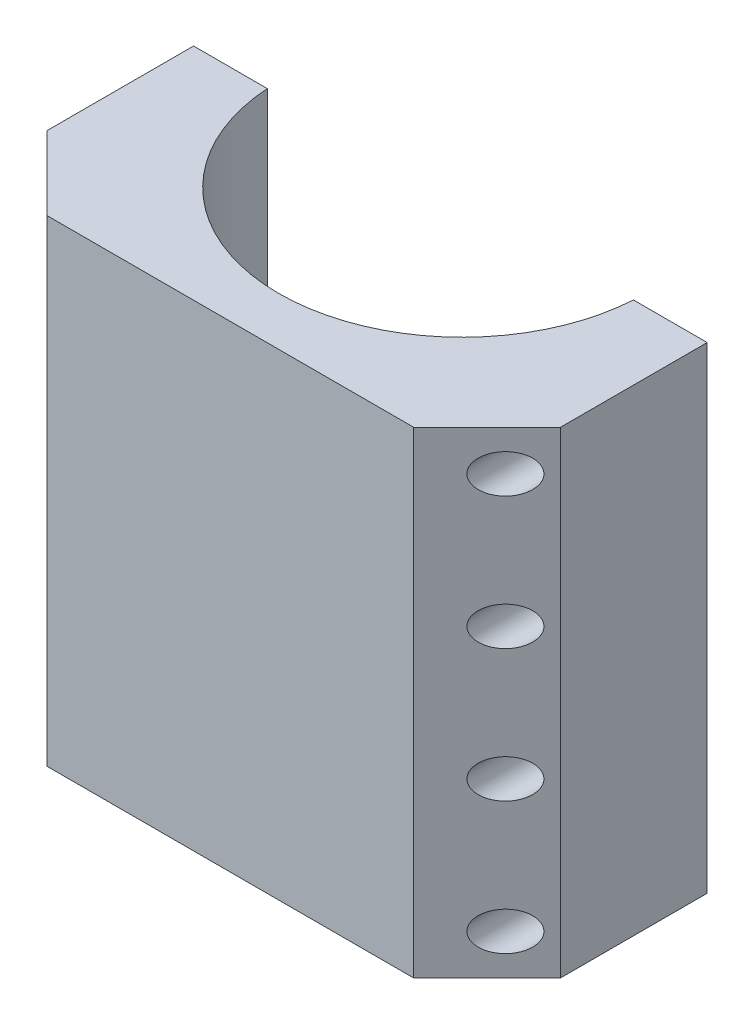
SolidWorks part; units mm, degrees
ref_plane "前视基准面" through (0, 0, 0) normal (0, 0, 1) x (1, 0, 0)
ref_plane "上视基准面" through (0, 0, 0) normal (0, 1, 0) x (1, 0, 0)
ref_plane "右视基准面" through (0, 0, 0) normal (1, 0, 0) x (0, 0, -1)
other "Configuration Table"
sketch "草图1" plane through (0, 0, 0) normal (0, 0, 1) x (1, 0, 0)
  line L1 (0, 0) -> (140, 0)
  line L2 (0, 0) -> (0, -130)
  line L3 (0, -130) -> (140, -130)
  line L4 (140, 0) -> (140, -130)
  dimension "D1" = 140
  dimension "D2" = 130
extrude "凸台-拉伸1" add sketch "草图1" along normal blind 60
chamfer "倒角1" distance 20 angle 45 2 edges at (140, -65, 60) (0, -65, 60)
sketch "草图2" plane through (0, 0, 0) normal (0, 1, 0) x (1, 0, 0)
  circle A2 centre (70, 3.2) radius 50
  dimension "D1" = 100
extrude "切除-拉伸1" cut sketch "草图2" against normal through all
sketch "草图7" plane through (0, 0, 60) normal (0, 0, 1) x (1, 0, 0)
  line L0 (0, 0) -> (20, 0) construction
  line L1 (0, -130) -> (0, 0) construction
  circle A0 centre (7.5, -11) radius 3
  circle A6 centre (132.5, -11) radius 3
  circle A7 centre (132.5, -47) radius 3
  circle A8 centre (132.5, -83) radius 3
  circle A9 centre (132.5, -119) radius 3
  circle A10 centre (7.5, -47) radius 3
  circle A11 centre (7.5, -83) radius 3
  circle A12 centre (7.5, -119) radius 3
  dimension "D3" = 6
  dimension "D1" = 11
  dimension "D2" = 7.5
  dimension "D4" = 2
  dimension "D5" = 4
extrude "切除-拉伸2" cut sketch "草图7" against normal through all
sketch "草图8" plane through (0, 0, 60) normal (0, 0, 1) x (1, 0, 0)
  circle A28 centre (7.5, -11) radius 5.25
  circle A29 centre (132.5, -11) radius 5.25
  circle A30 centre (132.5, -47) radius 5.25
  circle A31 centre (132.5, -83) radius 5.25
  circle A32 centre (132.5, -119) radius 5.25
  circle A33 centre (7.5, -47) radius 5.25
  circle A34 centre (7.5, -83) radius 5.25
  circle A35 centre (7.5, -119) radius 5.25
  dimension "D1" = 10.5
  dimension "D2" = 2
extrude "切除-拉伸3" cut sketch "草图8" against normal blind 35
